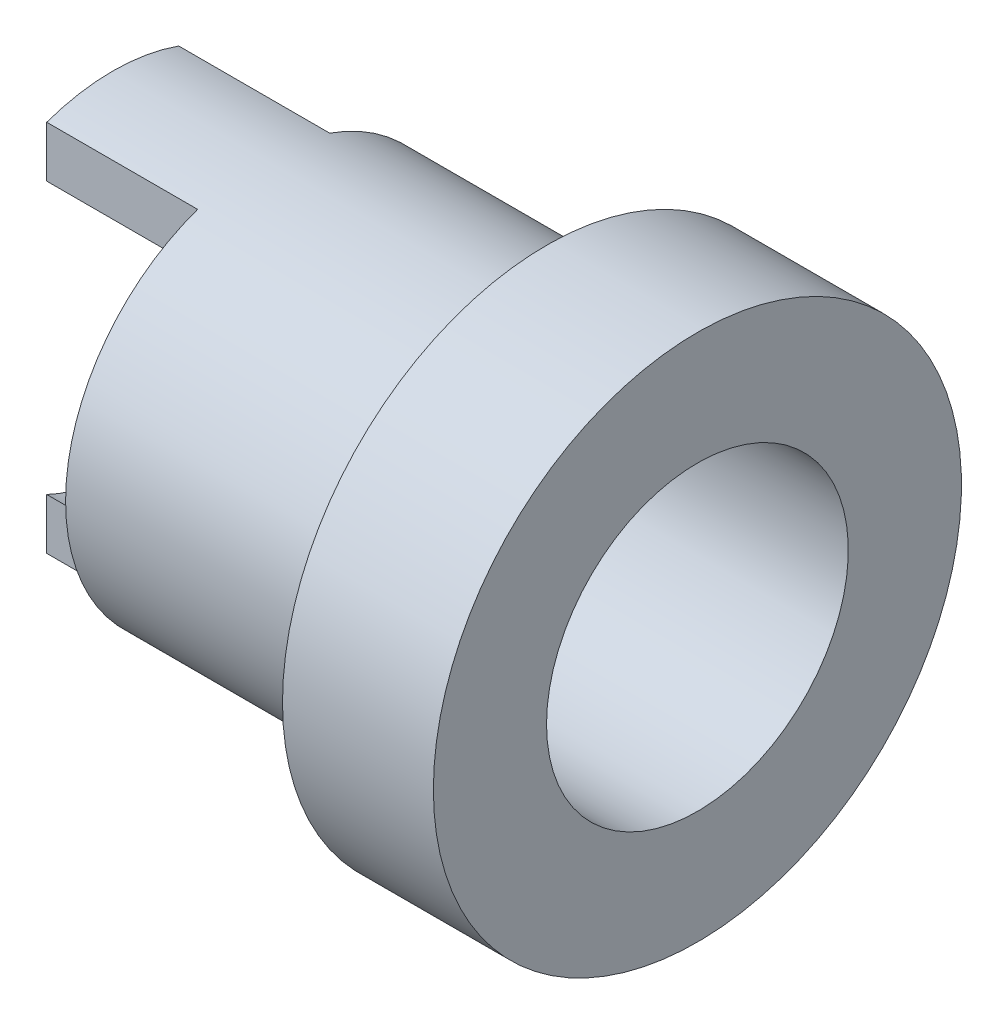
SolidWorks part; units mm, degrees
ref_plane "Front Plane" through (0, 0, 0) normal (0, 0, 1) x (1, 0, 0)
ref_plane "Top Plane" through (0, 0, 0) normal (0, 1, 0) x (1, 0, 0)
ref_plane "Right Plane" through (0, 0, 0) normal (1, 0, 0) x (0, 0, -1)
sketch "Sketch1" plane through (0, 0, 0) normal (0, 1, 0) x (1, 0, 0)
  line L0 (-5.1347, 0) -> (3.5301, 0) construction
  line L1 (0, 4) -> (0, 7)
  line L2 (0, 7) -> (-4, 7)
  line L3 (-4, 7) -> (-4, 5.25)
  line L4 (-4, 5.25) -> (-15.5, 5.25)
  line L5 (-15.5, 5.25) -> (-15.5, 4)
  line L6 (-15.5, 4) -> (0, 4)
  dimension "D1" = 4
  dimension "D2" = 7
  dimension "D3" = 5.25
  dimension "D4" = 4
  dimension "D5" = 11.5
revolve "Revolve1" add sketch "Sketch1" angle 360 about L0
sketch "Sketch2" plane through (-15.5, 0, 0) normal (-1, 0, 0) x (0, 0, 1)
  line L1 (-1.75, 4.9497) -> (-5.25, 4.9497)
  line L2 (-1.75, 4.9497) -> (-1.75, -4.9497)
  line L3 (-1.75, -4.9497) -> (-5.25, -4.9497)
  line L4 (-5.25, 4.9497) -> (-5.25, -4.9497)
  line L5 (1.75, 4.9497) -> (5.25, 4.9497)
  line L6 (1.75, 4.9497) -> (1.75, -4.9497)
  line L7 (1.75, -4.9497) -> (5.25, -4.9497)
  line L8 (5.25, 4.9497) -> (5.25, -4.9497)
  circle A0 centre (0, 0) radius 5.25 construction
  circle A1 centre (0, 0) radius 5.25 construction
  point P6 (-5.25, 0)
  dimension "D1" = 3.5
extrude "Cut-Extrude1" cut sketch "Sketch2" against normal blind 4
